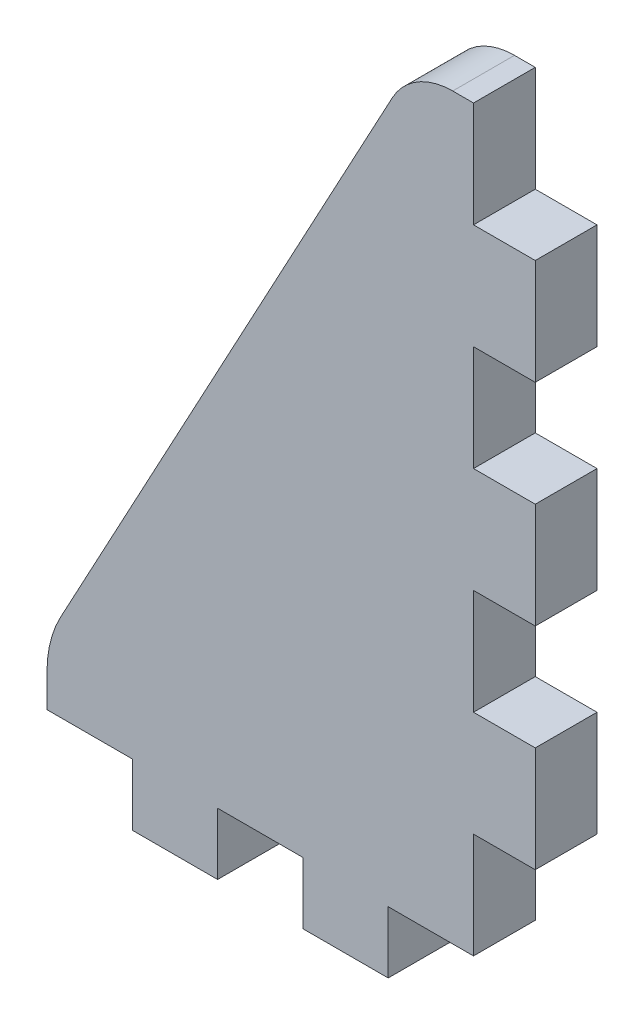
SolidWorks part; units mm, degrees
ref_plane "Ön Düzlem" through (0, 0, 0) normal (0, 0, 1) x (1, 0, 0)
ref_plane "Üst Düzlem" through (0, 0, 0) normal (0, 1, 0) x (1, 0, 0)
ref_plane "Sağ Düzlem" through (0, 0, 0) normal (1, 0, 0) x (0, 0, -1)
sketch "Sketch1" plane through (0, 0, 0) normal (0, 0, 1) x (1, 0, 0)
  line L0 (7.975, 17.5) -> (7.0663, 17.5)
  line L2 (10.675, -10.1857) -> (10.675, -5.5714)
  line L5 (7.975, -13.0738) -> (-1.094, 1.7934) construction
  line L6 (7.975, 13.0738) -> (-9.028, -14.8) construction
  line L7 (7.975, 17.5) -> (7.975, 12.8857)
  line L8 (4.245, -17.5) -> (0.515, -17.5)
  line L9 (-10.675, -14.8) -> (-6.945, -14.8)
  line L11 (-3.215, -17.5) -> (-6.945, -17.5)
  line L12 (-3.215, -14.8) -> (0.515, -14.8)
  line L13 (10.675, -0.9571) -> (10.675, 3.6571)
  line L14 (4.245, -14.8) -> (7.975, -14.8)
  line L15 (-6.945, -14.8) -> (-6.945, -17.5)
  line L16 (-3.215, -14.8) -> (-3.215, -17.5)
  line L17 (0.515, -14.8) -> (0.515, -17.5)
  line L18 (4.245, -14.8) -> (4.245, -17.5)
  line L19 (-10.675, -14.8) -> (-10.675, -13.3614)
  line L20 (7.975, 8.2714) -> (7.975, 3.6571)
  line L21 (-10.0766, -10.9896) -> (4.4253, 15.9231)
  line L22 (7.975, -0.9571) -> (7.975, -5.5714)
  line L24 (7.975, -10.1857) -> (7.975, -14.8)
  line L25 (7.975, 12.8857) -> (10.675, 12.8857)
  line L26 (7.975, 8.2714) -> (10.675, 8.2714)
  line L27 (7.975, 3.6571) -> (10.675, 3.6571)
  line L28 (7.975, -0.9571) -> (10.675, -0.9571)
  line L29 (7.975, -5.5714) -> (10.675, -5.5714)
  line L30 (7.975, -10.1857) -> (10.675, -10.1857)
  line L31 (10.675, 8.2714) -> (10.675, 12.8857)
  arc A0 (-10.0766, -10.9896) -> (-10.675, -13.3614) centre (-5.675, -13.3614) ccw
  arc A1 (7.0663, 17.5) -> (4.4253, 15.9231) centre (7.0663, 14.5) ccw
  point P0 (0, 0)
  dimension "D1" = 5
  dimension "D2" = 3
extrude "Boss-Extrude1" add sketch "Sketch1" against normal blind 2.7
